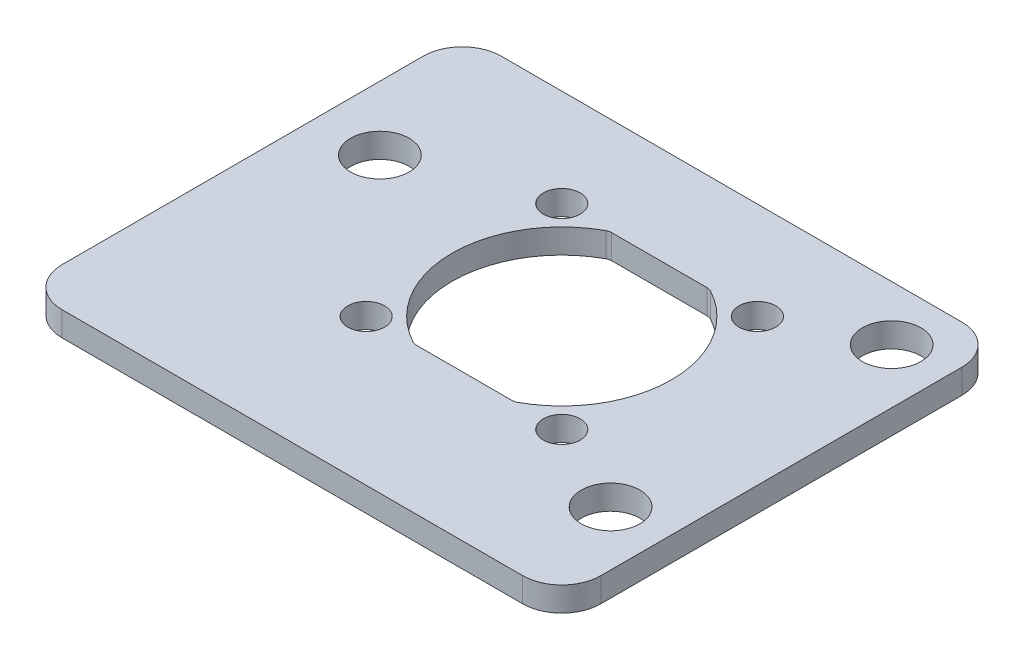
SolidWorks part; units mm, degrees
ref_plane "Front Plane" through (0, 0, 0) normal (0, 0, 1) x (1, 0, 0)
ref_plane "Top Plane" through (0, 0, 0) normal (0, 1, 0) x (1, 0, 0)
ref_plane "Right Plane" through (0, 0, 0) normal (1, 0, 0) x (0, 0, -1)
sketch "Sketch1" plane through (0, 0, 0) normal (0, 1, 0) x (1, 0, 0)
  line L0 (-6.364, 6.364) -> (6.364, -6.364) construction
  line L1 (-15.875, -12.7) -> (15.875, -12.7)
  line L2 (-15.875, -12.7) -> (-15.875, 12.7)
  line L3 (-15.875, 12.7) -> (15.875, 12.7)
  line L4 (15.875, -12.7) -> (15.875, 12.7)
  line L5 (-15.875, -12.7) -> (15.875, 12.7) construction
  line L6 (-15.875, 12.7) -> (15.875, -12.7) construction
  line L7 (-6.364, -6.364) -> (6.364, 6.364) construction
  line L8 (-6.364, 6.364) -> (-6.364, 12.7) construction
  line L9 (6.364, 6.364) -> (6.364, 12.7) construction
  line L10 (-15.875, 9.144) -> (-12.319, 9.144) construction
  line L11 (-12.319, 9.144) -> (-12.319, 12.7) construction
  line L12 (12.319, 12.7) -> (12.319, 9.144) construction
  line L13 (12.319, 9.144) -> (15.875, 9.144) construction
  line L14 (-12.319, 9.144) -> (0, 0) construction
  line L15 (12.319, -9.144) -> (12.319, -12.7) construction
  line L16 (12.319, -9.144) -> (15.875, -9.144) construction
  line L17 (-12.319, -12.7) -> (-12.319, -9.144) construction
  line L18 (-12.319, -9.144) -> (-15.875, -9.144) construction
  line L19 (-12.319, -9.144) -> (12.319, -9.144) construction
  circle A0 centre (0, 0) radius 7.1374
  circle A1 centre (-6.364, -6.364) radius 1.2
  circle A2 centre (-6.364, 6.364) radius 1.2
  circle A3 centre (6.364, 6.364) radius 1.2
  circle A4 centre (6.364, -6.364) radius 1.2
  circle A5 centre (-12.319, -9.144) radius 1.905
  circle A6 centre (-12.319, 9.144) radius 1.905
  circle A7 centre (12.319, 9.144) radius 1.905
  circle A8 centre (12.319, -9.144) radius 1.905
  circle A9 centre (0, 0) radius 10.9982 construction
  point P0 (0, 0)
  point P18 (0, 0)
  point P19 (0, 0)
  dimension "D1" = 14.2748
  dimension "D2" = 2.4
  dimension "D3" = 9
  dimension "D4" = 3.81
  dimension "D8" = 21.9964
  dimension "D5" = 25.4
  dimension "D6" = 31.75
  dimension "D7" = 3.556
extrude "Boss-Extrude1" add sketch "Sketch1" along normal blind 1.5875
sketch "Sketch2" plane through (0, 1.5875, 0) normal (0, 1, 0) x (1, 0, 0)
  line L0 (15.875, -12.7) -> (15.875, 12.7) construction
  line L5 (-15.875, -12.7) -> (15.875, -12.7)
  line L6 (-15.875, -12.7) -> (-15.875, -15.875)
  line L7 (-15.875, -15.875) -> (15.875, -15.875)
  line L8 (15.875, -12.7) -> (15.875, -15.875)
  dimension "D1" = 3.175
extrude "Boss-Extrude2" add sketch "Sketch2" against normal through all
sketch "Sketch5" plane through (0, 1.5875, 0) normal (0, 1, 0) x (1, 0, 0)
  line L0 (0, 0) -> (12.319, 9.144) construction
  line L5 (-19.177, 12.7) -> (-15.875, 12.7)
  line L6 (-15.875, -15.875) -> (15.875, -15.875) construction
  line L7 (-15.0097, 3.175) -> (0, 0) construction
  line L10 (-19.177, 12.7) -> (-19.177, -15.875)
  line L11 (-19.177, -15.875) -> (-15.875, -15.875)
  line L12 (-15.875, -15.875) -> (-15.875, 1.4779)
  line L13 (-15.875, 4.8721) -> (-15.875, 12.7)
  circle A1 centre (-12.319, 9.144) radius 1.905
  circle A3 centre (-12.319, -9.144) radius 1.905
  arc A5 (-15.875, 4.8721) -> (-15.875, 1.4779) centre (-15.0097, 3.175) ccw
  circle A6 centre (12.319, 9.144) radius 1.905 construction
  circle A7 centre (12.319, -9.144) radius 1.905 construction
  dimension "D1" = 3.302
  dimension "D2" = 19.05
extrude "Boss-Extrude4" add sketch "Sketch5" against normal through all
sketch "Sketch6" plane through (0, 1.5875, 0) normal (0, 1, 0) x (1, 0, 0)
  circle A2 centre (-15.0097, 3.175) radius 1.905
  arc A3 (-15.875, 4.8721) -> (-15.875, 1.4779) centre (-15.0097, 3.175) ccw construction
extrude "Cut-Extrude1" cut sketch "Sketch6" against normal through all
fillet "Fillet1" [suppressed] radius 2.54
sketch "Sketch3" plane through (0, 1.5875, 0) normal (0, 1, 0) x (1, 0, 0)
  line L0 (-3.2588, 6.35) -> (3.2588, 6.35)
  line L2 (3.2588, -6.35) -> (-3.2588, -6.35)
  arc A0 (-3.2588, -6.35) -> (3.2588, -6.35) centre (0, 0) ccw
  circle A1 centre (0, 0) radius 7.1374 construction
  arc A2 (3.2588, 6.35) -> (-3.2588, 6.35) centre (0, 0) ccw
  dimension "D1" = 12.7
extrude "Boss-Extrude3" add sketch "Sketch3" against normal through all
fillet "Fillet2" radius 0.635 4 edges at (-3.2588, 0.7937, -6.35) (3.2588, 0.7937, -6.35) (3.2588, 0.7937, 6.35) (-3.2588, 0.7937, 6.35)
fillet "Fillet3" radius 2.54 4 edges at (15.875, 0.7937, 15.875) (15.875, 0.7937, -12.7) (-19.177, 0.7937, -12.7) (-19.177, 0.7937, 15.875)
